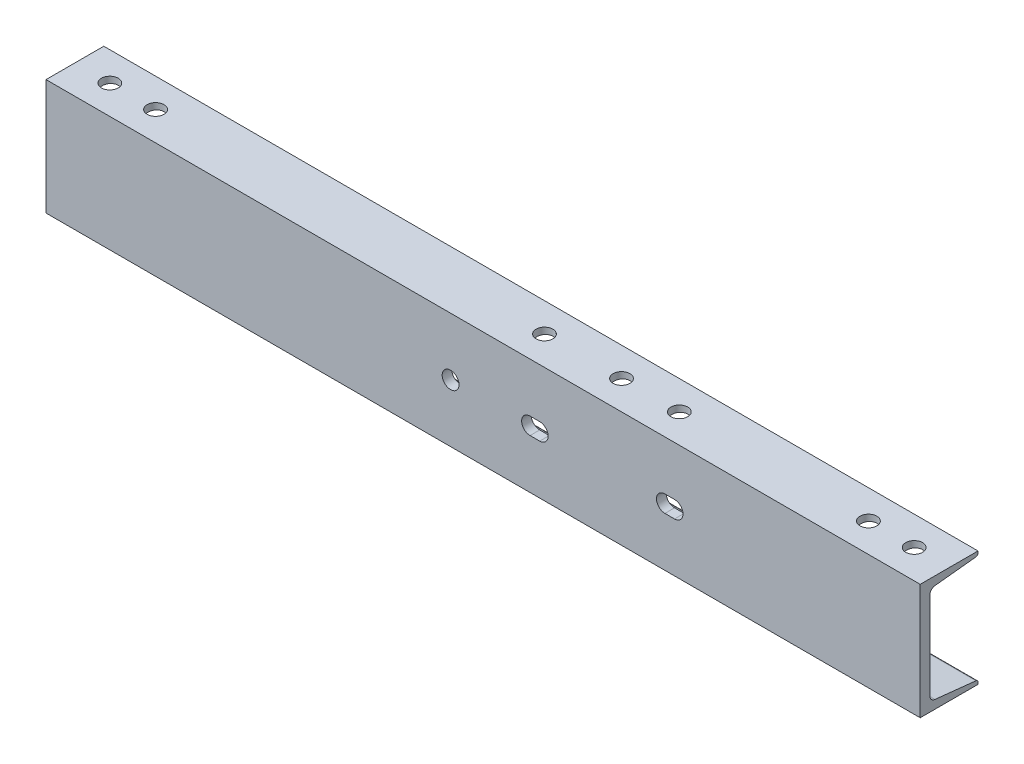
SolidWorks part; units mm, degrees
ref_plane "Front Plane" through (0, 0, 0) normal (0, 0, 1) x (1, 0, 0)
ref_plane "Top Plane" through (0, 0, 0) normal (0, 1, 0) x (1, 0, 0)
ref_plane "Right Plane" through (0, 0, 0) normal (1, 0, 0) x (0, 0, -1)
sketch "Sketch1" plane through (0, 0, 0) normal (1, 0, 0) x (0, 0, -1)
  line L0 (-48.8061, -76.2) -> (-48.8061, 76.2)
  line L1 (-48.8061, 76.2) -> (27.3939, 76.2)
  line L2 (-48.8061, -76.2) -> (27.3939, -76.2)
  line L3 (4.3561, -67.4878) -> (-21.0439, -67.4878) construction
  line L4 (-36.1061, 57.3918) -> (-36.1061, -57.3918)
  line L5 (27.3939, 76.2) -> (27.3939, 73.7107)
  line L6 (27.3939, -76.2) -> (27.3939, -73.7107)
  line L7 (-29.2881, 64.9695) -> (24.6667, 70.6797)
  line L8 (-29.2881, -64.9695) -> (24.6667, -70.6797)
  arc A0 (-36.1061, -57.3918) -> (-29.2881, -64.9695) centre (-28.4861, -57.3918) ccw
  arc A1 (-36.1061, 57.3918) -> (-29.2881, 64.9695) centre (-28.4861, 57.3918) cw
  arc A2 (27.3939, 73.7107) -> (24.6667, 70.6797) centre (24.3459, 73.7107) cw
  arc A3 (27.3939, -73.7107) -> (24.6667, -70.6797) centre (24.3459, -73.7107) ccw
  dimension "D1" = 76.2
  dimension "D2" = 12.7
  dimension "D3" = 152.4
extrude "Boss-Extrude1" add sketch "Sketch1" along normal mid plane 1152.525
sketch "Sketch5" plane through (0, -76.2, 0) normal (0, -1, 0) x (1, 0, 0)
  line L0 (687.9131, 10.7061) -> (42.799, 10.7061) construction
  line L2 (576.2625, 48.8061) -> (576.2625, -27.3939) construction
  line L3 (-576.2625, 48.8061) -> (-576.2625, -27.3939) construction
  line L5 (576.2625, 48.8061) -> (-576.2625, 48.8061) construction
  circle A0 centre (530.225, 10.7061) radius 11.1125
  circle A1 centre (469.9, 10.7061) radius 11.1125
  circle A2 centre (42.799, 10.7061) radius 11.1125
  circle A3 centre (220.599, 10.7061) radius 11.1125
  circle A5 centre (144.399, 10.7061) radius 11.1125
  circle A6 centre (-530.225, 10.7061) radius 11.1125
  circle A7 centre (-469.9, 10.7061) radius 11.1125
  circle A10 centre (280.924, 10.7061) radius 11.1125 [skipped]
  circle A11 centre (84.074, 10.7061) radius 11.1125 [skipped]
  dimension "D2" = 22.225
  dimension "D4" = 60.325
  dimension "D12" = 76.2
  dimension "D16" = 22.225
  dimension "D17" = 101.6
  dimension "D8" = 309.626
  dimension "D3" = 46.0375
  dimension "D10" = 46.0375
  dimension "D11" = 38.1
  dimension "D5" = 2
  dimension "D7" = 2
  dimension "D9" = 2
extrude "Cut-Extrude3" cut sketch "Sketch5" against normal up to surface (152.4 mm away) up to face at (0, 76.2, 10.7061)
sketch "Sketch6" plane through (0, 0, 36.1061) normal (0, 0, -1) x (-1, 0, 0)
  line L0 (576.2625, 0) -> (-576.2625, 0) construction
  line L1 (576.2625, -57.3918) -> (576.2625, 57.3918) construction
  line L2 (-576.2625, -57.3918) -> (-576.2625, 57.3918) construction
  line L3 (-74.6125, 0) -> (-61.9125, 0) construction
  line L4 (-74.6125, 11.1125) -> (-61.9125, 11.1125)
  line L5 (-74.6125, -11.1125) -> (-61.9125, -11.1125)
  line L7 (-239.7125, 0) -> (-252.4125, 0) construction
  line L8 (-239.7125, -11.1125) -> (-252.4125, -11.1125)
  line L9 (-239.7125, 11.1125) -> (-252.4125, 11.1125)
  circle A0 centre (42.8625, 0) radius 11.1125
  arc A1 (-74.6125, 11.1125) -> (-74.6125, -11.1125) centre (-74.6125, 0) ccw
  arc A2 (-239.7125, -11.1125) -> (-239.7125, 11.1125) centre (-239.7125, 0) ccw
  arc A3 (-61.9125, -11.1125) -> (-61.9125, 11.1125) centre (-61.9125, 0) ccw
  arc A4 (-252.4125, 11.1125) -> (-252.4125, -11.1125) centre (-252.4125, 0) ccw
  point P10 (-68.2625, 0)
  point P18 (-246.0625, 0)
  dimension "D1" = 22.225
  dimension "D2" = 533.4
  dimension "D3" = 638.175
  dimension "D4" = 12.7
  dimension "D5" = 177.8
  dimension "D6" = 12.7
extrude "Cut-Extrude4" cut sketch "Sketch6" against normal through all
